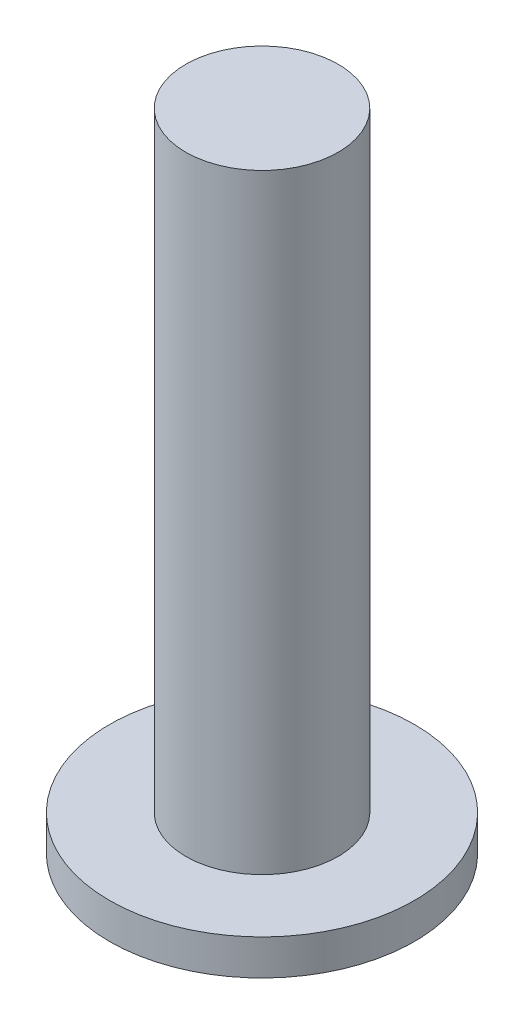
SolidWorks part; units mm, degrees
ref_plane "Front Plane" through (0, 0, 0) normal (0, 0, 1) x (1, 0, 0)
ref_plane "Top Plane" through (0, 0, 0) normal (0, 1, 0) x (1, 0, 0)
ref_plane "Right Plane" through (0, 0, 0) normal (1, 0, 0) x (0, 0, -1)
sketch "Sketch1" plane through (0, 0, 0) normal (0, 1, 0) x (1, 0, 0)
  circle A0 centre (0, 0) radius 1.5
  dimension "D1" = 3
extrude "Boss-Extrude1" add sketch "Sketch1" along normal blind 0.35
sketch "Sketch2" plane through (0, 0.35, 0) normal (0, 1, 0) x (1, 0, 0)
  circle A0 centre (0, 0) radius 0.75
  dimension "D1" = 1.5
extrude "Boss-Extrude2" add sketch "Sketch2" along normal blind 6
